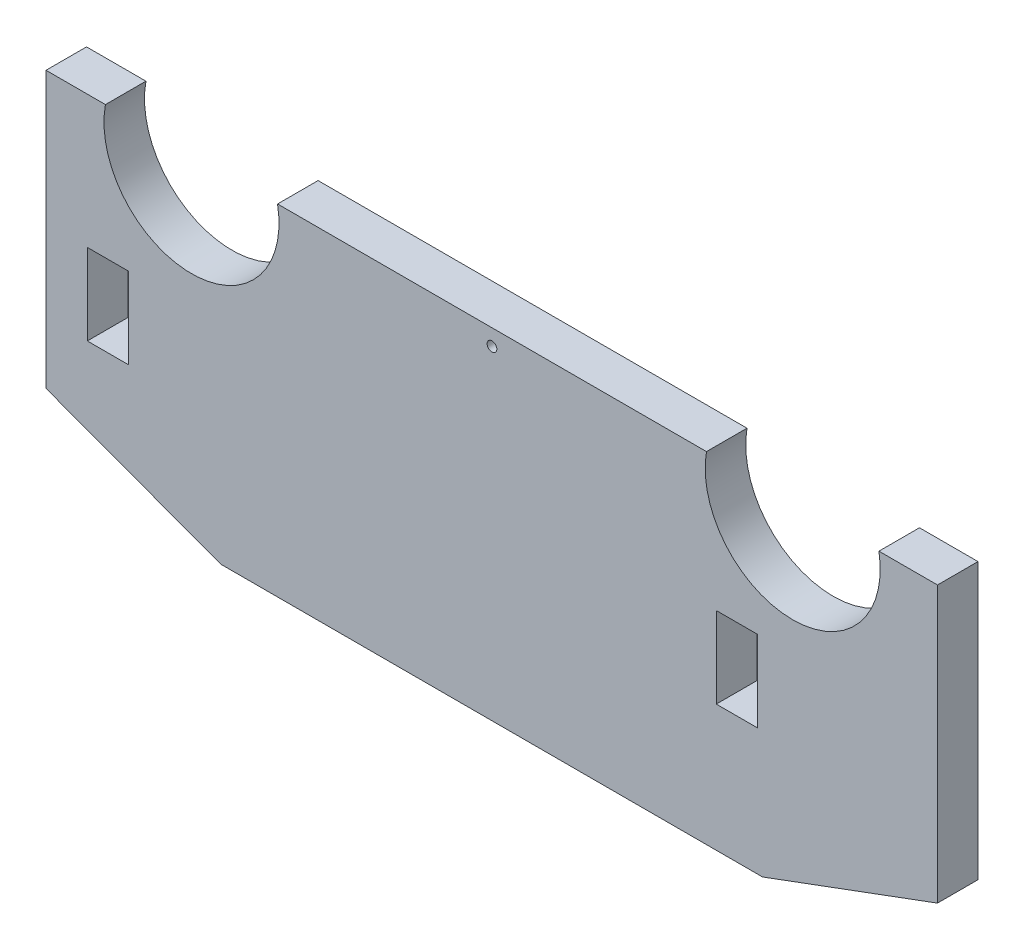
SolidWorks part; units mm, degrees
ref_plane "Front Plane" through (0, 0, 0) normal (0, 0, 1) x (1, 0, 0)
ref_plane "Top Plane" through (0, 0, 0) normal (0, 1, 0) x (1, 0, 0)
ref_plane "Right Plane" through (0, 0, 0) normal (1, 0, 0) x (0, 0, -1)
sketch "Sketch1" plane through (0, 0, 0) normal (0, 0, 1) x (1, 0, 0)
  line L1 (-34.925, -9.525) -> (34.925, -9.525)
  line L2 (-34.925, -9.525) -> (-34.925, 9.525)
  line L3 (-34.925, 9.525) -> (34.925, 9.525)
  line L4 (34.925, -9.525) -> (34.925, 9.525)
  line L5 (-34.925, -9.525) -> (34.925, 9.525) construction
  line L6 (-34.925, 9.525) -> (34.925, -9.525) construction
  point P0 (0, 0)
  dimension "D1" = 69.85
  dimension "D2" = 19.05
extrude "main body" add sketch "Sketch1" along normal blind 3.175
sketch "Sketch9" plane through (0, 0, 3.175) normal (0, 0, 1) x (1, 0, 0)
  line L0 (-34.925, -9.525) -> (-34.925, -12.065)
  line L1 (-34.925, -12.065) -> (-21.2149, -17.145)
  line L2 (-21.2149, -17.145) -> (0, -17.145)
  line L3 (0, -17.145) -> (0, -9.525)
  line L4 (-34.925, -9.525) -> (34.925, -9.525) construction
  line L5 (0, -9.525) -> (-34.925, -9.525)
  dimension "D1" = 7.62
  dimension "D2" = 2.54
extrude "chin feature" add sketch "Sketch9" against normal blind 3.175
mirror "mirror of chin feature" about plane through (0, 0, 0) normal (1, 0, 0) of "chin feature"
sketch "Sketch10" plane through (0, 0, 3.175) normal (0, 0, 1) x (1, 0, 0)
  line L1 (-31.689, -0.8754) -> (-28.4632, -0.8754)
  line L2 (-31.689, -0.8754) -> (-31.689, -7.2254)
  line L3 (-31.689, -7.2254) -> (-28.4632, -7.2254)
  line L4 (-28.4632, -0.8754) -> (-28.4632, -7.2254)
  line L5 (-31.689, -0.8754) -> (-28.4632, -7.2254) construction
  line L6 (-31.689, -7.2254) -> (-28.4632, -0.8754) construction
  line L7 (17.5928, -0.8754) -> (20.8186, -0.8754)
  line L8 (17.5928, -0.8754) -> (17.5928, -7.2254)
  line L9 (17.5928, -7.2254) -> (20.8186, -7.2254)
  line L10 (20.8186, -0.8754) -> (20.8186, -7.2254)
  line L11 (17.5928, -0.8754) -> (20.8186, -7.2254) construction
  line L12 (17.5928, -7.2254) -> (20.8186, -0.8754) construction
  point P0 (-30.0761, -4.0504)
  point P5 (19.2057, -4.0504)
  dimension "D1" = 3.2258
  dimension "D2" = 6.35
  dimension "D3" = 3.2258
  dimension "D4" = 6.35
extrude "cut for tabs" cut sketch "Sketch10" against normal through all
sketch "Sketch11" plane through (0, 0, 3.175) normal (0, 0, 1) x (1, 0, 0)
  line B0 (-23.5766, 18.5161) -> (-26.3706, 18.5161)
  line B1 (-26.3706, 18.5161) -> (-26.3706, 14.5201)
  line B2 (-20.7826, 14.5654) -> (-20.7826, 18.5161)
  line B3 (-20.7826, 18.5161) -> (-23.5766, 18.5161)
  arc B4 (-26.3706, 14.5201) -> (-20.7826, 14.5654) centre (-23.5258, 8.2799) ccw
  line B5 (23.5305, 18.5857) -> (20.7365, 18.5857)
  line B6 (20.7365, 18.5857) -> (20.7365, 14.5897)
  line B7 (26.3245, 14.635) -> (26.3245, 18.5857)
  line B8 (26.3245, 18.5857) -> (23.5305, 18.5857)
  arc B9 (20.7365, 14.5897) -> (26.3245, 14.635) centre (23.5813, 8.3495) ccw
sketch_block_instance "servo_topAperture_SG90-1"
sketch_block "Block1"
sketch_block_instance "Block1-1"
extrude "cut for lip motor aperture" cut sketch "Sketch11" against normal through all
sketch "Sketch12" plane through (0, 0, 3.175) normal (0, 0, 1) x (1, 0, 0)
  line L0 (0, 0) -> (0.0215, 9.525) construction
  line L1 (16.8248, 9.525) -> (-16.7818, 9.525) construction
  circle A0 centre (0.0186, 8.255) radius 0.381
  dimension "D1" = 0.762
  dimension "D2" = 1.27
extrude "Cut-Extrude1" cut sketch "Sketch12" against normal through all
